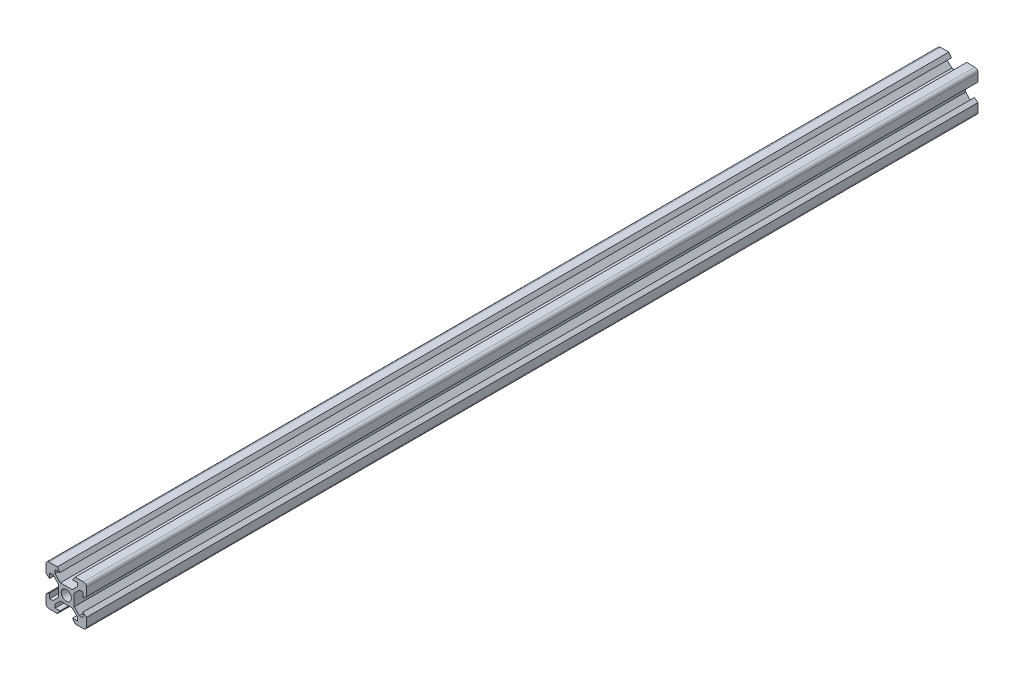
SolidWorks part; units mm, degrees
ref_plane "前视基准面" through (0, 0, 0) normal (0, 0, 1) x (1, 0, 0)
ref_plane "上视基准面" through (0, 0, 0) normal (0, 1, 0) x (1, 0, 0)
ref_plane "右视基准面" through (0, 0, 0) normal (1, 0, 0) x (0, 0, -1)
sketch "草图1" plane through (0, 0, 0) normal (0, 0, 1) x (1, 0, 0)
  line L0 (16.8101, 19.3214) -> (19.4, 21.9114) construction
  line L1 (14.8, 34.8214) -> (18.9, 34.8214)
  line L2 (13.3, 33.3214) -> (13.3, 29.2214)
  line L3 (14.8, 14.8214) -> (18.9, 14.8214)
  line L4 (33.3, 33.3214) -> (33.3, 29.2214)
  line L7 (27.2, 27.7315) -> (29.7899, 30.3214) construction
  line L8 (33.3, 29.2214) -> (31.5, 27.9214)
  line L9 (28.8, 31.3114) -> (26.2101, 28.7214)
  line L10 (31.5, 30.3214) -> (31.5, 27.9214)
  line L11 (29.7899, 30.3214) -> (31.5, 30.3214)
  line L12 (26.2101, 28.7214) -> (28.8, 31.3114) construction
  line L13 (27.2, 27.7315) -> (29.7899, 30.3214)
  line L15 (20.3899, 28.7214) -> (26.2101, 28.7214) construction
  line L18 (18.9, 34.8214) -> (20.2, 33.0214)
  line L19 (27.7, 34.8214) -> (26.4, 33.0214)
  line L20 (26.4, 33.0214) -> (28.8, 33.0214)
  line L21 (28.8, 33.0214) -> (28.8, 31.3114)
  line L22 (26.2101, 28.7214) -> (20.3899, 28.7214)
  line L25 (20.3899, 28.7214) -> (17.8, 31.3114)
  line L26 (17.8, 31.3114) -> (17.8, 33.0214)
  line L27 (17.8, 33.0214) -> (20.2, 33.0214)
  line L28 (27.2, 21.9114) -> (27.2, 27.7315)
  line L29 (29.7899, 19.3214) -> (27.2, 21.9114)
  line L30 (31.5, 19.3214) -> (29.7899, 19.3214)
  line L31 (31.5, 21.7214) -> (31.5, 19.3214)
  line L32 (33.3, 20.4214) -> (31.5, 21.7214)
  line L33 (27.7, 14.8214) -> (26.4, 16.6214)
  line L34 (28.8, 16.6214) -> (26.4, 16.6214)
  line L35 (28.8, 18.3315) -> (28.8, 16.6214)
  line L36 (26.2101, 20.9214) -> (28.8, 18.3315)
  line L37 (20.3899, 20.9214) -> (26.2101, 20.9214)
  line L38 (17.8, 18.3315) -> (20.3899, 20.9214)
  line L39 (17.8, 16.6214) -> (17.8, 18.3315)
  line L40 (20.2, 16.6214) -> (17.8, 16.6214)
  line L41 (18.9, 14.8214) -> (20.2, 16.6214)
  line L42 (13.3, 20.4214) -> (15.1, 21.7214)
  line L43 (15.1, 19.3214) -> (15.1, 21.7214)
  line L44 (16.8101, 19.3214) -> (15.1, 19.3214)
  line L45 (19.4, 21.9114) -> (16.8101, 19.3214)
  line L46 (19.4, 27.7315) -> (19.4, 21.9114)
  line L47 (16.8101, 30.3214) -> (19.4, 27.7315)
  line L48 (15.1, 30.3214) -> (16.8101, 30.3214)
  line L49 (15.1, 27.9214) -> (15.1, 30.3214)
  line L50 (13.3, 29.2214) -> (15.1, 27.9214)
  line L51 (27.7, 34.8214) -> (31.8, 34.8214)
  line L52 (33.3, 20.4214) -> (33.3, 16.3214)
  line L53 (13.3, 20.4214) -> (13.3, 16.3214)
  line L54 (27.7, 14.8214) -> (31.8, 14.8214)
  circle A0 centre (23.3, 24.8214) radius 2.5
  arc A1 (14.8, 34.8214) -> (13.3, 33.3214) centre (14.8, 33.3214) ccw
  arc A2 (33.3, 33.3214) -> (31.8, 34.8214) centre (31.8, 33.3214) ccw
  arc A3 (31.8, 14.8214) -> (33.3, 16.3214) centre (31.8, 16.3214) ccw
  arc A4 (14.8, 14.8214) -> (13.3, 16.3214) centre (14.8, 16.3214) cw
  point P11 (33.3, 34.8214)
  point P18 (33.3, 14.8214)
  dimension "D3" = 5
  dimension "D1" = 1.5
  dimension "D4" = 1.5
  dimension "D5" = 1.5
  dimension "D7" = 1.5
  dimension "D2" = 20
  dimension "D6" = 4
extrude "凸台-拉伸1" add sketch "草图1" along normal blind 440
